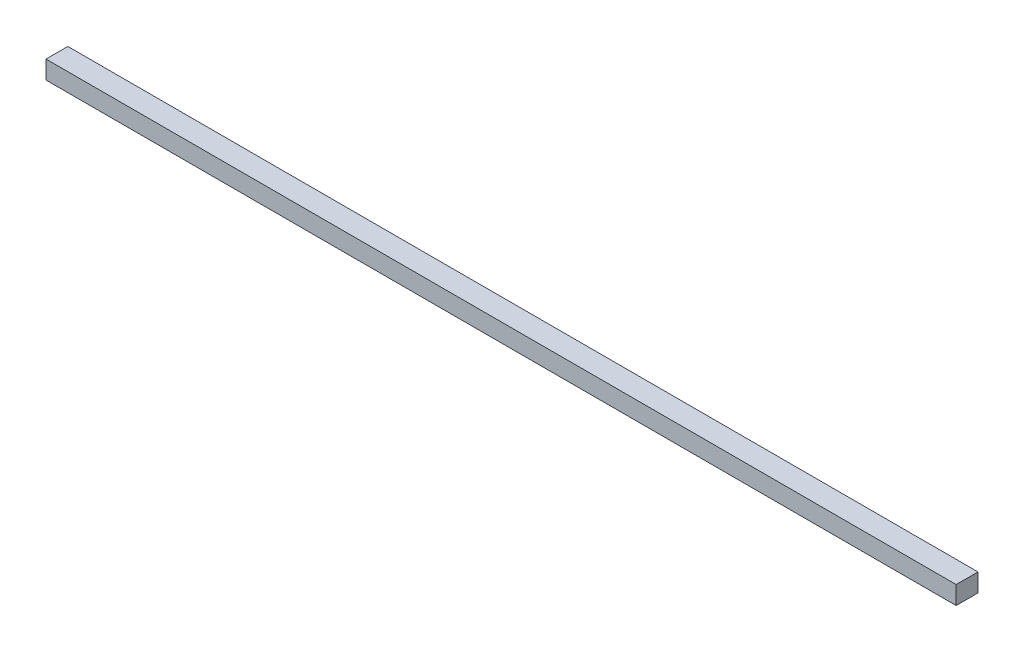
SolidWorks part; units mm, degrees
ref_plane "Front Plane" through (0, 0, 0) normal (0, 0, 1) x (1, 0, 0)
ref_plane "Top Plane" through (0, 0, 0) normal (0, 1, 0) x (1, 0, 0)
ref_plane "Right Plane" through (0, 0, 0) normal (1, 0, 0) x (0, 0, -1)
sketch "Sketch1" plane through (0, 0, 0) normal (0, 1, 0) x (1, 0, 0)
  line L1 (250, -6) -> (-250, -6)
  line L2 (250, -6) -> (250, 6)
  line L3 (250, 6) -> (-250, 6)
  line L4 (-250, -6) -> (-250, 6)
  line L5 (250, -6) -> (-250, 6) construction
  line L6 (250, 6) -> (-250, -6) construction
  point P0 (0, 0)
  dimension "D1" = 12
  dimension "D2" = 500
extrude "Boss-Extrude1" add sketch "Sketch1" along normal blind 10
